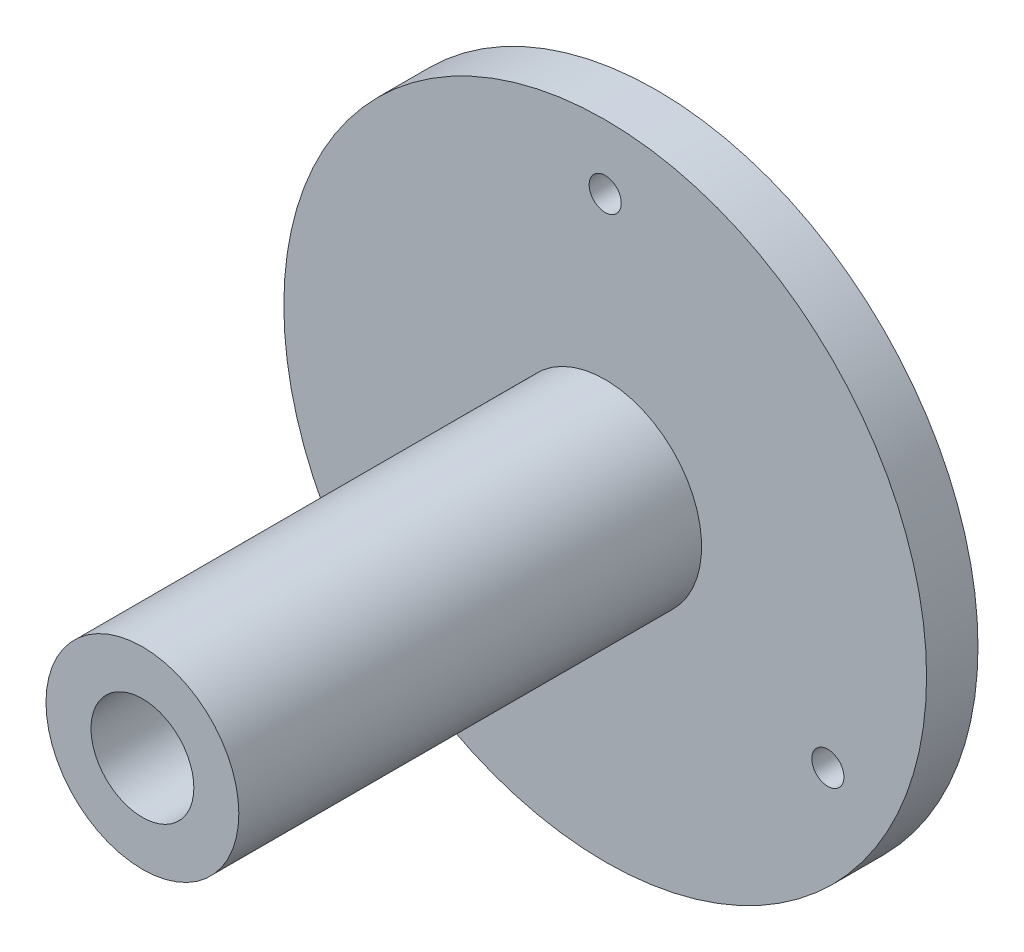
SolidWorks part; units mm, degrees
ref_plane "Front Plane" through (0, 0, 0) normal (0, 0, 1) x (1, 0, 0)
ref_plane "Top Plane" through (0, 0, 0) normal (0, 1, 0) x (1, 0, 0)
ref_plane "Right Plane" through (0, 0, 0) normal (1, 0, 0) x (0, 0, -1)
sketch "Sketch1" plane through (0, 0, 10) normal (0, 0, 1) x (1, 0, 0)
  circle A0 centre (0, 0) radius 8
  circle A1 centre (0, 0) radius 15
  dimension "D1" = 30
  dimension "D2" = 16
extrude "Boss-Extrude1" add sketch "Sketch1" along normal blind 80
sketch "Sketch2" plane through (0, 0, 10) normal (0, 0, -1) x (-1, 0, 0)
  circle A0 centre (0, 0) radius 50
  circle A1 centre (0, 0) radius 12.5
  dimension "D1" = 100
extrude "Boss-Extrude2" add sketch "Sketch2" against normal blind 8
sketch "Sketch3" plane through (0, 0, 18) normal (0, 0, 1) x (1, 0, 0)
  circle A0 centre (0, 40) radius 2.5
  circle A1 centre (0, 0) radius 50 construction
  dimension "D1" = 5
  dimension "D2" = 40
extrude "Cut-Extrude1" cut sketch "Sketch3" against normal blind 8
pattern_circular "CirPattern1" count 3 every 120 about axis through (0, 0, 0) along (0, 0, 1) of "Cut-Extrude1"
